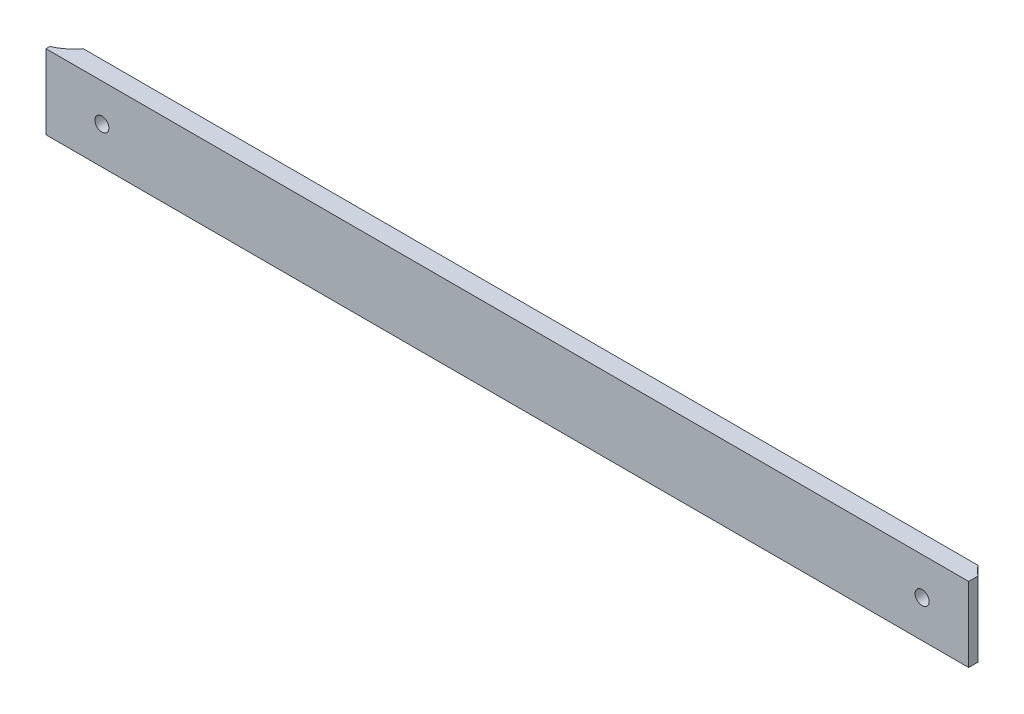
SolidWorks part; units mm, degrees
material "AISI 1010 Steel, hot rolled bar"
ref_plane "Front Plane" through (0, 0, 0) normal (0, 0, 1) x (1, 0, 0)
ref_plane "Top Plane" through (0, 0, 0) normal (0, 1, 0) x (1, 0, 0)
ref_plane "Right Plane" through (0, 0, 0) normal (1, 0, 0) x (0, 0, -1)
sketch "Sketch1" plane through (0, 0, 0) normal (0, 1, 0) x (1, 0, 0)
  line L0 (0, 64.5186) -> (0, -64.5186) construction
  line L1 (-152.4, -9.525) -> (152.4, -9.525)
  line L2 (-158.75, -15.875) -> (155.575, -15.875)
  line L3 (-152.4, -15.875) -> (152.4, -15.875) construction
  line L4 (-158.75, -14.5497) -> (-158.75, -15.875)
  line L5 (155.575, -12.7) -> (155.575, -15.875)
  arc A0 (-158.75, -14.5497) -> (-152.4, -9.525) centre (-165.1, 0) ccw
  arc A1 (155.575, -12.7) -> (152.4, -9.525) centre (165.1, 0) cw
  point P5 (0, 0)
  dimension "D1" = 31.75
  dimension "D2" = 330.2
  dimension "D4" = 6.35
  dimension "D5" = 9.525
  dimension "D3" = 6.35
extrude "Base" add sketch "Sketch1" along normal mid plane 25.4
sketch "Sketch2" plane through (0, 0, 9.525) normal (0, 0, -1) x (-1, 0, 0)
  line L1 (0, 27.0975) -> (0, -27.0975) construction
  line L2 (0, 55) -> (0, -55) construction
  circle A0 centre (-139.7, 0) radius 4.826
  circle A1 centre (139.7, 0) radius 4.826
  point P7 (0, 0)
  dimension "D1" = 9.652
  dimension "D2" = 279.4
extrude "Hole" [suppressed] cut sketch "Sketch2" against normal through all
hole_wizard "3/16 (0.1875) Diameter Hole1" positions "Sketch4" profile "Sketch3" hole size "3/16" standard "Ansi Inch" end condition through all
sketch "Sketch4" plane through (0, 0, 15.875) normal (0, 0, 1) x (1, 0, 0)
  line L0 (0, 63.2822) -> (0, -144.4872) construction
  point P0 (-139.7, 0)
  point P7 (139.7, 0)
  dimension "D1" = 279.4
sketch "Sketch3" plane through (-139.7, 0, 15.875) normal (1, 0, 0) x (0, -1, 0)
  line L0 (0, 0) -> (0, 6.35)
  line L1 (0, 6.35) -> (2.3812, 6.35)
  line L2 (2.3812, 6.35) -> (2.3812, 0)
  line L5 (2.3812, 0) -> (0, 0)
  line L11 (0, -6.35) -> (0, 107.95) construction
  dimension "Thru Hole Dia." = 4.7625
  dimension "Thru Hole Depth" = 6.35
